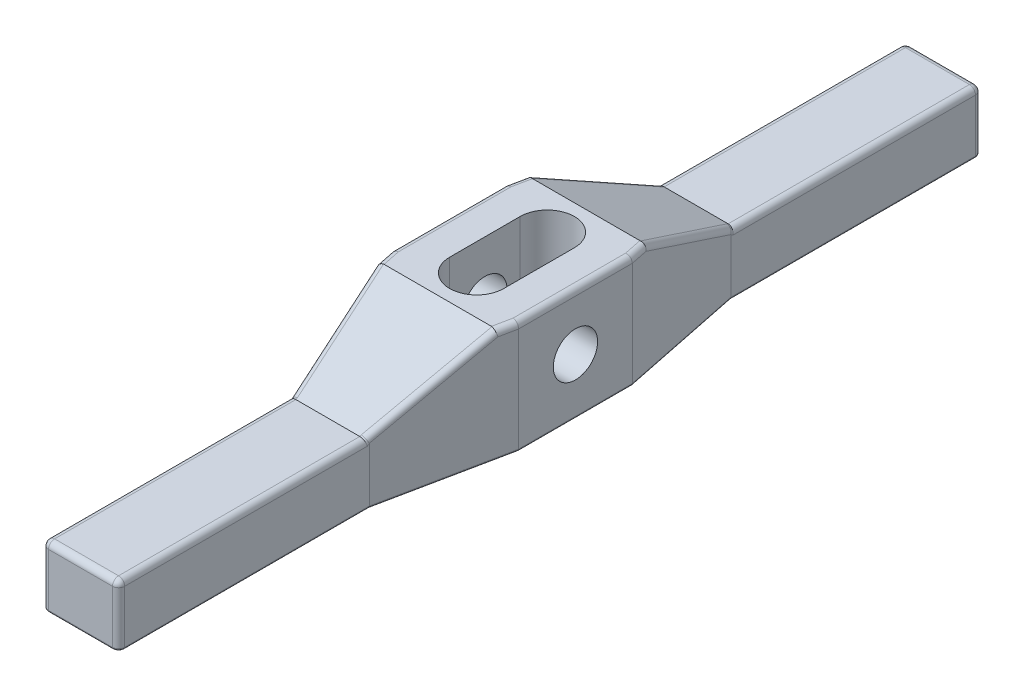
SolidWorks part; units mm, degrees
material "Alloy Steel"
ref_plane "Front Plane" through (0, 0, 0) normal (0, 0, 1) x (1, 0, 0)
ref_plane "Top Plane" through (0, 0, 0) normal (0, 1, 0) x (1, 0, 0)
ref_plane "Right Plane" through (0, 0, 0) normal (1, 0, 0) x (0, 0, -1)
sketch "Sketch1" plane through (0, 0, 0) normal (0, 1, 0) x (1, 0, 0)
  line L0 (0, 0) -> (68.8474, 0) construction
  line L1 (0, 0) -> (0, 75.643) construction
  line L2 (-9.525, 107.95) -> (9.525, 107.95)
  line L3 (9.525, 107.95) -> (9.525, 45.212)
  line L4 (9.525, 45.212) -> (15.875, 14.2245)
  line L5 (15.875, 14.2245) -> (15.875, -14.2245)
  line L6 (9.525, -45.212) -> (15.875, -14.2245)
  line L7 (9.525, -107.95) -> (9.525, -45.212)
  line L8 (-9.525, -107.95) -> (9.525, -107.95)
  line L9 (-9.525, -107.95) -> (-9.525, -45.212)
  line L10 (-9.525, -45.212) -> (-15.875, -14.2245)
  line L11 (-15.875, 14.2245) -> (-15.875, -14.2245)
  line L12 (-9.525, 45.212) -> (-15.875, 14.2245)
  line L13 (-9.525, 107.95) -> (-9.525, 45.212)
  line L14 (-6.7818, 8.8265) -> (-6.7818, -8.8265)
  line L15 (6.7818, 8.8265) -> (6.7818, -8.8265)
  arc A0 (6.7818, 8.8265) -> (-6.7818, 8.8265) centre (0, 8.8265) ccw
  arc A1 (-6.7818, -8.8265) -> (6.7818, -8.8265) centre (0, -8.8265) ccw
  dimension "D1" = 19.05
  dimension "D2" = 215.9
  dimension "D3" = 31.75
  dimension "D4" = 62.738
  dimension "D5" = 28.449
  dimension "D6" = 17.653
  dimension "D7" = 13.5636
extrude "Extrude1" add sketch "Sketch1" along normal blind 28.067
sketch "Sketch2" plane through (15.875, 0, 0) normal (1, 0, 0) x (0, 0, -1)
  line L0 (0, 0) -> (0, 25.2428) construction
  line L1 (-14.2245, 0) -> (14.2245, 0) construction
  line L2 (107.95, 28.067) -> (18.5674, 28.067)
  line L3 (14.2245, 28.067) -> (45.212, 28.067) construction
  line L4 (18.5674, 28.067) -> (46.075, 15.24)
  line L5 (46.075, 15.24) -> (107.95, 15.24)
  line L6 (107.95, 28.067) -> (107.95, 0) construction
  line L7 (107.95, 15.24) -> (107.95, 28.067)
  line L8 (45.212, 0) -> (107.95, 0) construction
  line L9 (-107.95, 15.24) -> (-107.95, 28.067)
  line L10 (-46.075, 15.24) -> (-107.95, 15.24)
  line L11 (-18.5674, 28.067) -> (-46.075, 15.24)
  line L12 (-107.95, 28.067) -> (-18.5674, 28.067)
  dimension "D1" = 18.5674
  dimension "D2" = 25
  dimension "D3" = 15.24
extrude "Cut-Extrude1" cut sketch "Sketch2" against normal through all
sketch "Sketch3" plane through (15.875, 0, 0) normal (1, 0, 0) x (0, 0, -1)
  line L0 (-14.2245, 0) -> (14.2245, 0) construction
  circle A0 centre (0, 13.9446) radius 5.5436
  dimension "D1" = 11.0871
  dimension "D2" = 13.9446
extrude "Cut-Extrude2" cut sketch "Sketch3" against normal through all
fillet "Fillet1" radius 1.524 4 edges at (-9.525, 7.62, -107.95) (9.525, 7.62, -107.95) (9.525, 7.62, 107.95) (-9.525, 7.62, 107.95)
fillet "Fillet2" radius 0.508 16 edges at (-9.525, 0, 75.819) (-9.0786, 0, 107.5036) (0, 0, 107.95) (9.0786, 0, 107.5036) (-9.525, 0, -75.819) (-9.0786, 0, -107.5036) (0, 0, -107.95) (9.0786, 0, -107.5036) (-12.7, 0, -29.7183) (-15.875, 0, 0) (-12.7, 0, 29.7183) (9.525, 0, 75.819) (12.7, 0, 29.7183) (15.875, 0, 0) (12.7, 0, -29.7183) (9.525, 0, -75.819)
fillet "Fillet3" radius 1.524 24 edges at (-9.0786, 15.24, 107.5036) (0, 15.24, 107.95) (9.0786, 15.24, 107.5036) (-9.525, 15.24, -76.2505) (-9.0786, 15.24, -107.5036) (0, 15.24, -107.95) (9.0786, 15.24, -107.5036) (-12.255, 21.8547, -31.8897) (-15.43, 28.067, -16.396) (-15.43, 28.067, 16.396) (-15.875, 28.067, 0) (-12.255, 21.8547, 31.8897) (-9.525, 15.24, 76.2505) (9.525, 15.24, 76.2505) (12.255, 21.8547, 31.8897) (15.43, 28.067, 16.396) (15.875, 28.067, 0) (15.43, 28.067, -16.396) (12.255, 21.8547, -31.8897) (9.525, 15.24, -76.2505) (-9.525, 15.4412, -45.6435) (9.525, 15.4412, -45.6435) (-9.525, 15.4412, 45.6435) (9.525, 15.4412, 45.6435)
